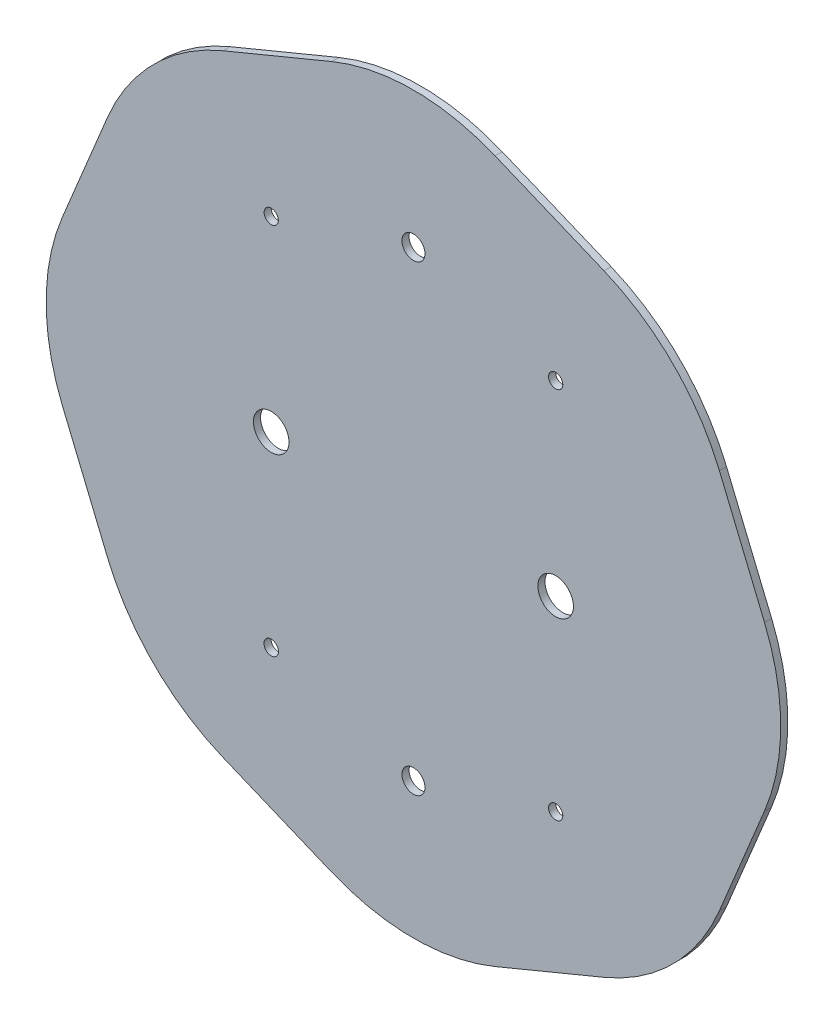
SolidWorks part; units mm, degrees
material "PVC Rigid"
ref_plane "Front Plane" through (0, 0, 0) normal (0, 0, 1) x (1, 0, 0)
ref_plane "Top Plane" through (0, 0, 0) normal (0, 1, 0) x (1, 0, 0)
ref_plane "Right Plane" through (0, 0, 0) normal (1, 0, 0) x (0, 0, -1)
sketch "Sketch1" plane through (0, 0, 0) normal (0, 0, 1) x (1, 0, 0)
  line L1 (-2.2961, 9.8728) -> (-5.3576, 8.6047)
  line L2 (-8.6047, 5.3576) -> (-9.8728, 2.2961)
  line L3 (-9.8728, -2.2961) -> (-8.6047, -5.3576)
  line L4 (-5.3576, -8.6047) -> (-2.2961, -9.8728)
  line L5 (2.2961, -9.8728) -> (5.3576, -8.6047)
  line L6 (8.6047, -5.3576) -> (9.8728, -2.2961)
  line L7 (9.8728, 2.2961) -> (8.6047, 5.3576)
  line L8 (5.3576, 8.6047) -> (2.2961, 9.8728)
  circle A0 centre (0, 0) radius 10.8239 construction
  arc A1 (-5.3576, 8.6047) -> (-8.6047, 5.3576) centre (-3.0615, 3.0615) ccw
  arc A2 (-9.8728, 2.2961) -> (-9.8728, -2.2961) centre (-4.3296, 0) ccw
  arc A3 (-8.6047, -5.3576) -> (-5.3576, -8.6047) centre (-3.0615, -3.0615) ccw
  arc A4 (-2.2961, -9.8728) -> (2.2961, -9.8728) centre (0, -4.3296) ccw
  arc A5 (5.3576, -8.6047) -> (8.6047, -5.3576) centre (3.0615, -3.0615) ccw
  arc A6 (9.8728, -2.2961) -> (9.8728, 2.2961) centre (4.3296, 0) ccw
  arc A7 (8.6047, 5.3576) -> (5.3576, 8.6047) centre (3.0615, 3.0615) ccw
  arc A8 (-2.2961, 9.8728) -> (2.2961, 9.8728) centre (0, 4.3296) cw
  point P27 (0, 10.8239)
  dimension "D1" = 6
  dimension "D2" = 20
extrude "Boss-Extrude1" add sketch "Sketch1" along normal blind 0.2
sketch "Sketch2" plane through (0, 0, 0) normal (0, 0, -1) x (-1, 0, 0)
  line L0 (4, -5.25) -> (4, 5.25) construction
  line L1 (0, -6.5) -> (0, 6.5) construction
  circle A0 centre (0, -6.5) radius 0.3239
  circle A1 centre (-4, -5.25) radius 0.2
  circle A2 centre (4, -5.25) radius 0.2036
  circle A3 centre (4, 5.25) radius 0.2
  circle A4 centre (0, 6.5) radius 0.3239
  circle A5 centre (-4, 5.25) radius 0.2
  circle A6 centre (4, 0) radius 0.5
  circle A7 centre (-4, 0) radius 0.5
  dimension "D1" = 1
extrude "Cut-Extrude1" cut sketch "Sketch2" against normal through all contours A3 | A4 | A5 | A7 | A6 | A2 | A0 | A1
